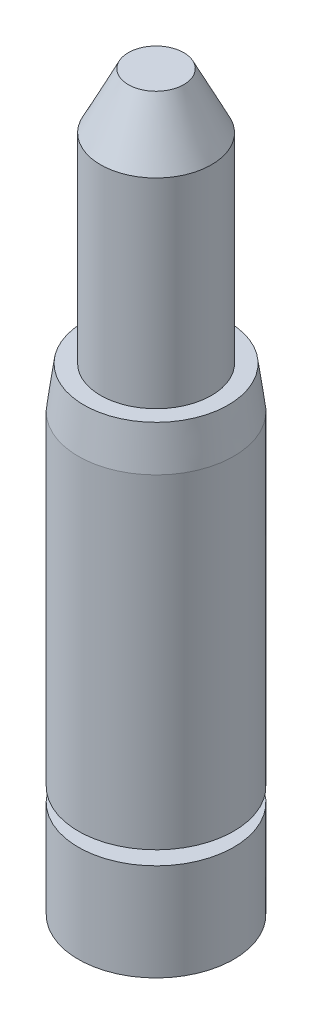
SolidWorks part; units mm, degrees
ref_plane "Front Plane" through (0, 0, 0) normal (0, 0, 1) x (1, 0, 0)
ref_plane "Top Plane" through (0, 0, 0) normal (0, 1, 0) x (1, 0, 0)
ref_plane "Right Plane" through (0, 0, 0) normal (1, 0, 0) x (0, 0, -1)
sketch "Sketch1" plane through (0, 0, 0) normal (0, 0, 1) x (1, 0, 0)
  line L0 (0, 0) -> (0, 167.64)
  line L1 (0, 167.64) -> (6.35, 167.64)
  line L2 (6.35, 167.64) -> (12.7, 154.94)
  line L3 (12.7, 154.94) -> (12.7, 109.22)
  line L4 (12.7, 109.22) -> (16.51, 109.22)
  line L5 (17.78, 99.695) -> (17.78, 25.4)
  line L6 (17.78, 25.4) -> (12.7, 25.4)
  line L7 (12.7, 25.4) -> (12.7, 22.225)
  line L8 (12.7, 22.225) -> (17.78, 22.225)
  line L9 (17.78, 22.225) -> (17.78, 0)
  line L10 (17.78, 0) -> (0, 0)
  line L11 (16.51, 109.22) -> (17.78, 99.695)
  point P7 (17.78, 109.22)
  dimension "D1" = 167.64
  dimension "D2" = 12.7
  dimension "D3" = 6.35
  dimension "D4" = 17.78
  dimension "D5" = 12.7
  dimension "D6" = 3.175
  dimension "D7" = 17.78
  dimension "D8" = 17.78
  dimension "D9" = 83.82
  dimension "D10" = 25.4
  dimension "D11" = 12.7
  dimension "D12" = 1.27
  dimension "D13" = 9.525
revolve "Revolve1" add sketch "Sketch1" angle 360 about L0
